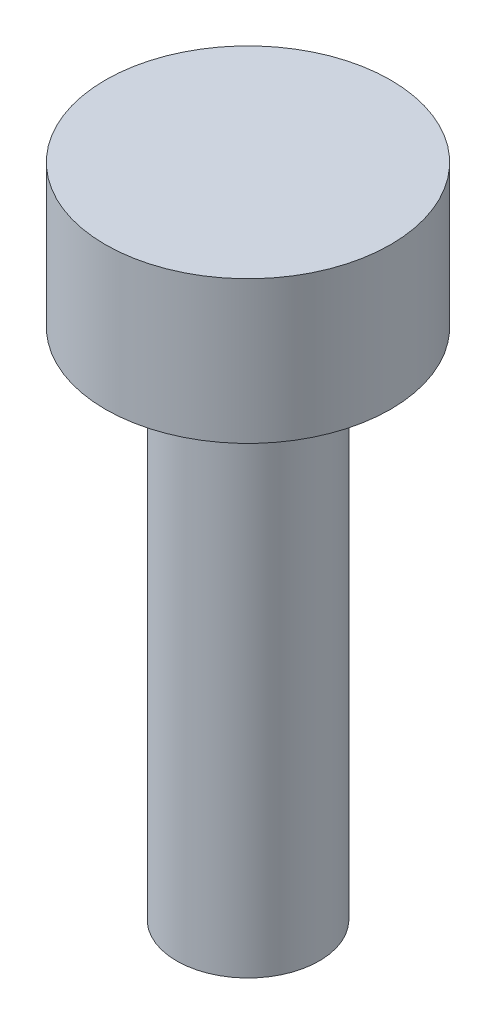
SolidWorks part; units mm, degrees
ref_plane "Front Plane" through (0, 0, 0) normal (0, 0, 1) x (1, 0, 0)
ref_plane "Top Plane" through (0, 0, 0) normal (0, 1, 0) x (1, 0, 0)
ref_plane "Right Plane" through (0, 0, 0) normal (1, 0, 0) x (0, 0, -1)
sketch "Sketch1" plane through (0, 0, 0) normal (0, 1, 0) x (1, 0, 0)
  circle A0 centre (0, 0) radius 5
extrude "Boss-Extrude1" add sketch "Sketch1" along normal blind 36
sketch "Sketch2" plane through (0, 36, 0) normal (0, 1, 0) x (1, 0, 0)
  circle A31 centre (0, 0) radius 10
extrude "Boss-Extrude2" add sketch "Sketch2" along normal blind 10
